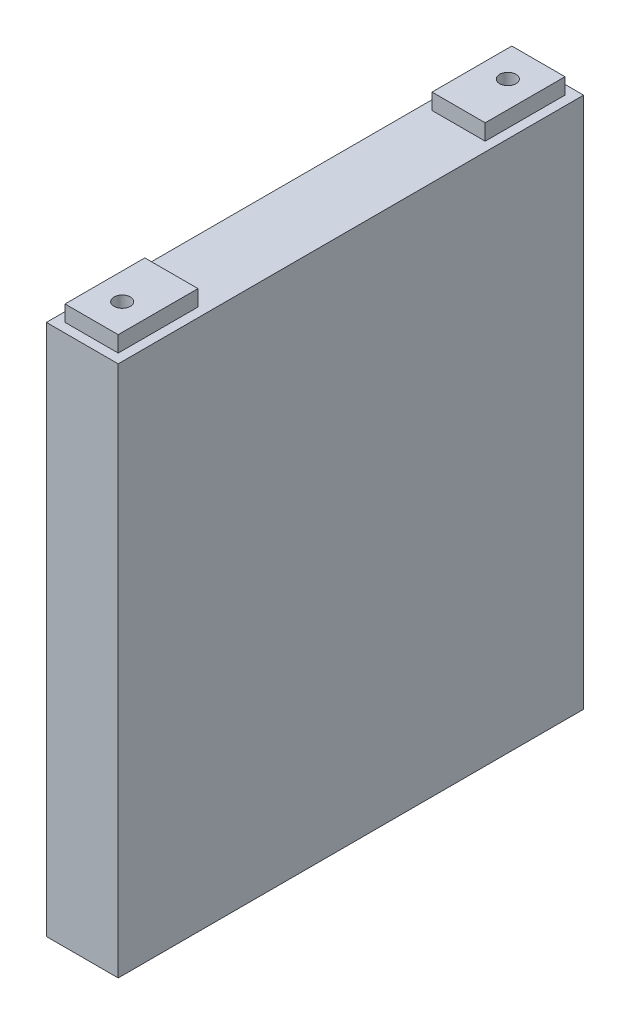
SolidWorks part; units mm, degrees
ref_plane "Front Plane" through (0, 0, 0) normal (0, 0, 1) x (1, 0, 0)
ref_plane "Top Plane" through (0, 0, 0) normal (0, 1, 0) x (1, 0, 0)
ref_plane "Right Plane" through (0, 0, 0) normal (1, 0, 0) x (0, 0, -1)
sketch "Sketch1" plane through (0, 0, 0) normal (0, 1, 0) x (1, 0, 0)
  line L1 (-13.5, -87.5) -> (13.5, -87.5)
  line L2 (-13.5, -87.5) -> (-13.5, 87.5)
  line L3 (-13.5, 87.5) -> (13.5, 87.5)
  line L4 (13.5, -87.5) -> (13.5, 87.5)
  line L5 (-13.5, -87.5) -> (13.5, 87.5) construction
  line L6 (-13.5, 87.5) -> (13.5, -87.5) construction
  point P0 (0, 0)
  dimension "D1" = 27
  dimension "D2" = 175
extrude "Boss-Extrude1" add sketch "Sketch1" along normal blind 200
sketch "Sketch2" plane through (0, 200, 0) normal (0, 1, 0) x (1, 0, 0)
  line L0 (0, 0) -> (0, 69) construction
  line L1 (0, 0) -> (0, -69) construction
  line L2 (13.5, 87.5) -> (-13.5, 87.5) construction
  line L3 (-10, -84) -> (10, -84)
  line L4 (-10, -84) -> (-10, -54)
  line L5 (-10, -54) -> (10, -54)
  line L6 (10, -84) -> (10, -54)
  line L7 (-10, -84) -> (10, -54) construction
  line L8 (-10, -54) -> (10, -84) construction
  line L9 (-10, 54) -> (10, 54)
  line L10 (-10, 54) -> (-10, 84)
  line L11 (-10, 84) -> (10, 84)
  line L12 (10, 54) -> (10, 84)
  line L13 (-10, 54) -> (10, 84) construction
  line L14 (-10, 84) -> (10, 54) construction
  line L15 (0, 69) -> (0, 72.5) construction
  line L16 (0, -69) -> (0, -72.5) construction
  circle A0 centre (0, -72.5) radius 3.0719
  circle A1 centre (0, 72.5) radius 3.0719
  point P18 (0, 0)
  point P19 (0, -71.5484)
  point P20 (0, 75.712)
  point P21 (0, 71.1669)
  dimension "D4" = 6.1438
  dimension "D1" = 30
  dimension "D2" = 20
  dimension "D3" = 3.5
  dimension "D5" = 145
extrude "Boss-Extrude2" add sketch "Sketch2" along normal blind 6
